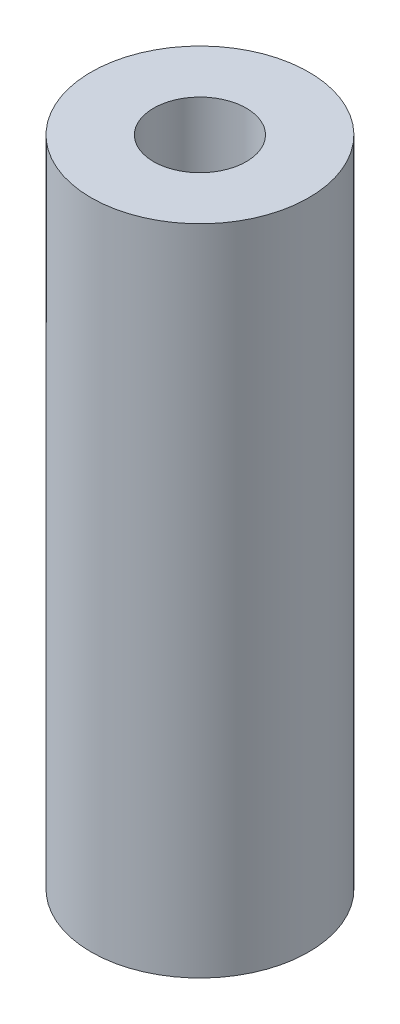
SolidWorks part; units mm, degrees
ref_plane "Front Plane" through (0, 0, 0) normal (0, 0, 1) x (1, 0, 0)
ref_plane "Top Plane" through (0, 0, 0) normal (0, 1, 0) x (1, 0, 0)
ref_plane "Right Plane" through (0, 0, 0) normal (1, 0, 0) x (0, 0, -1)
sketch "Sketch1" plane through (0, 0, 0) normal (0, 1, 0) x (1, 0, 0)
  circle A0 centre (0, 0) radius 3.175
  dimension "D1" = 6.35
extrude "Boss-Extrude1" add sketch "Sketch1" along normal blind 19.05
hole_wizard "Tap Drill for #6-32 Tap1" positions "Sketch3" profile "Sketch2" hole size "#6-32" standard "ANSI Inch" end condition through all
sketch "Sketch3" plane through (0, 19.05, 0) normal (0, 1, 0) x (1, 0, 0)
  point P0 (0, 0)
sketch "Sketch2" plane through (0, 19.05, 0) normal (1, 0, 0) x (0, 0, 1)
  line L0 (0, 0) -> (0, 19.05)
  line L1 (0, 19.05) -> (1.3525, 19.05)
  line L2 (1.3525, 19.05) -> (1.3525, 0)
  line L5 (1.3525, 0) -> (0, 0)
  line L11 (0, -6.35) -> (0, 107.95) construction
  dimension "Thru Hole Dia." = 2.7051
  dimension "Thru Hole Depth" = 19.05
